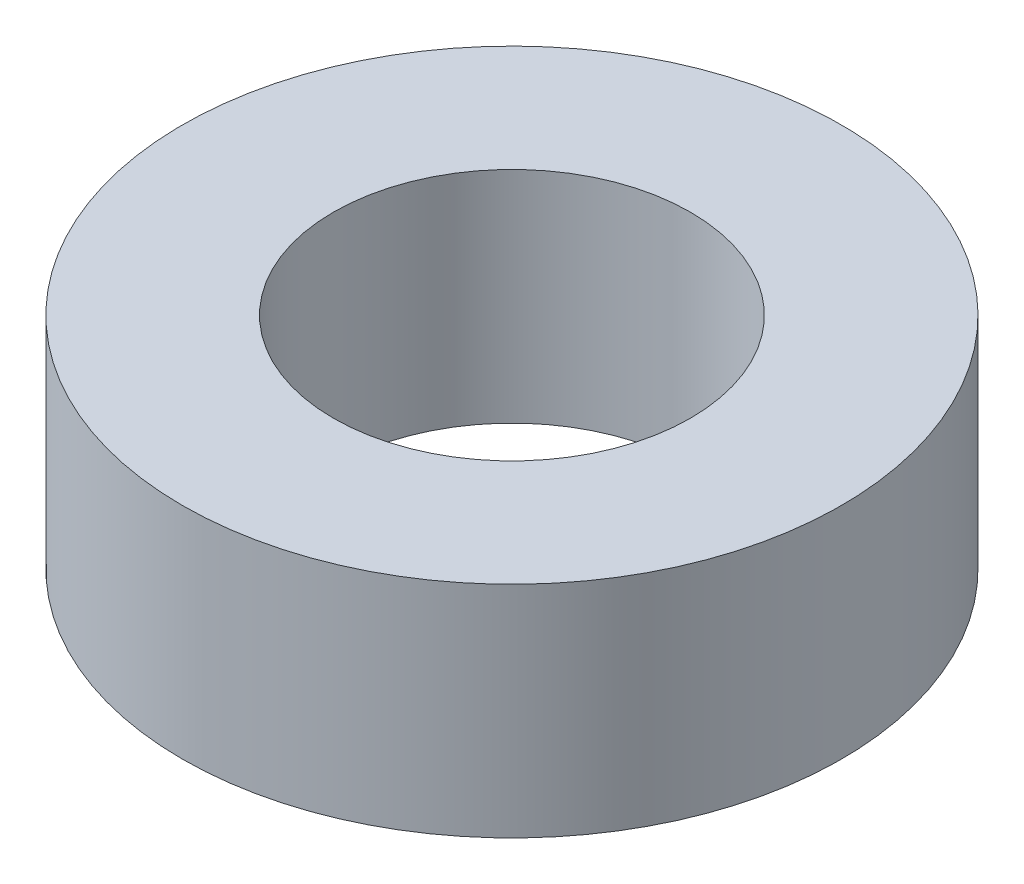
SolidWorks part; units mm, degrees
ref_plane "Front Plane" through (0, 0, 0) normal (0, 0, 1) x (1, 0, 0)
ref_plane "Top Plane" through (0, 0, 0) normal (0, 1, 0) x (1, 0, 0)
ref_plane "Right Plane" through (0, 0, 0) normal (1, 0, 0) x (0, 0, -1)
sketch "Sketch1" plane through (0, 0, 0) normal (0, 1, 0) x (1, 0, 0)
  circle A0 centre (0, 0) radius 3.25
  circle A1 centre (0, 0) radius 6
  dimension "D1" = 6.5
  dimension "D2" = 12
extrude "Boss-Extrude1" add sketch "Sketch1" along normal blind 4
